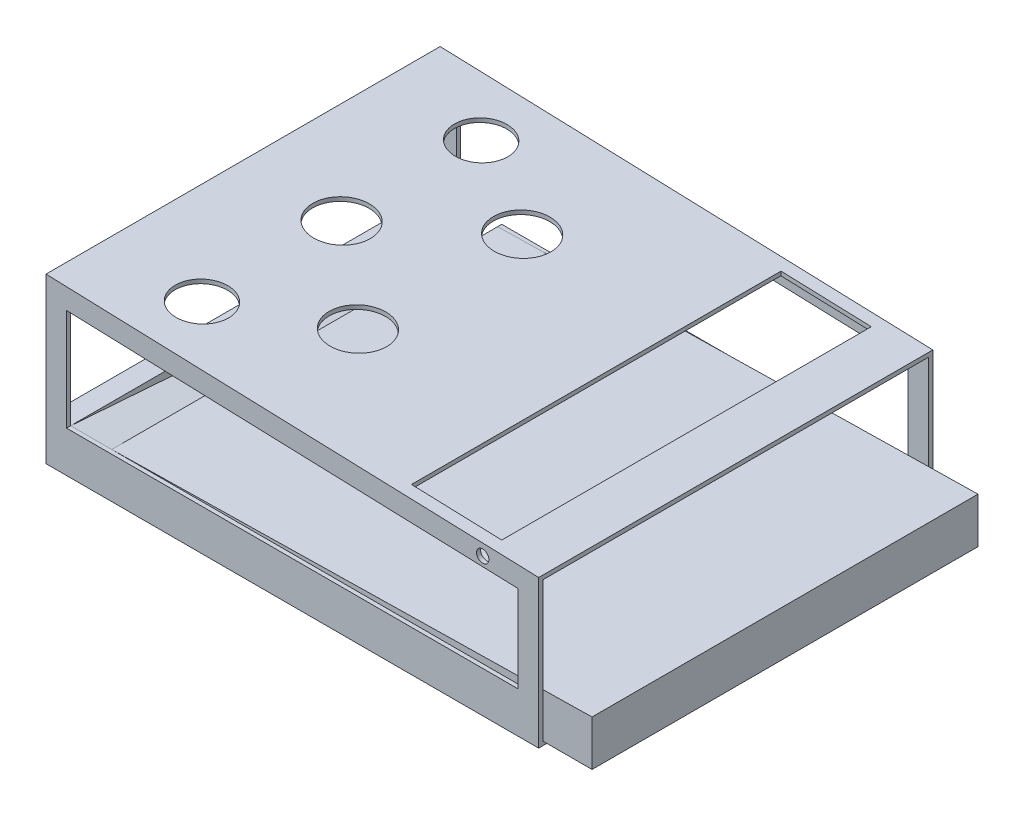
SolidWorks part; units mm, degrees
material "Balsa"
ref_plane "Front Plane" through (0, 0, 0) normal (0, 0, 1) x (1, 0, 0)
ref_plane "Top Plane" through (0, 0, 0) normal (0, 1, 0) x (1, 0, 0)
ref_plane "Right Plane" through (0, 0, 0) normal (1, 0, 0) x (0, 0, -1)
sketch "Sketch1" plane through (0, 0, 0) normal (0, 0, 1) x (1, 0, 0)
  line L0 (-373.9816, 0) -> (388.0184, 0)
  line L1 (-373.9816, 0) -> (-373.9816, 254)
  line L2 (388.0184, 0) -> (388.0184, 228.6)
  line L3 (-373.9816, 254) -> (388.0184, 228.6)
  line L4 (388.0184, 228.6) -> (-373.9816, 228.6) construction
  line L5 (-348.1349, 0) -> (-348.1349, 22.3158) construction
  line L6 (-348.1349, 22.3158) -> (-373.9816, 22.3158) construction
  point P4 (0, 0)
  point P5 (7.0184, 0)
  dimension "D1" = 762
  dimension "D2" = 254
  dimension "D3" = 228.6
extrude "Boss-Extrude1" add sketch "Sketch1" against normal blind 609.6
shell "Shell1" thickness 6.35
sketch "Sketch2" plane through (0, 0, 0) normal (0, 0, 1) x (1, 0, 0)
  line L0 (-342.2316, 221.174) -> (356.2684, 197.8907)
  line L2 (356.2684, 197.8907) -> (356.2684, 63.5)
  line L3 (356.2684, 63.5) -> (-342.2316, 63.5)
  line L4 (-342.2316, 63.5) -> (-342.2316, 221.174)
  line L5 (-373.9816, 0) -> (388.0184, 0) construction
  line L6 (388.0184, 0) -> (388.0184, 228.6) construction
  line L7 (388.0184, 228.6) -> (-373.9816, 254) construction
  line L8 (-373.9816, 254) -> (-373.9816, 0) construction
  point P3 (356.2684, 130.6953)
  dimension "D1" = 63.5
  dimension "D2" = 31.75
  dimension "D3" = 31.75
  dimension "D4" = 31.75
extrude "Cut-Extrude1" cut sketch "Sketch2" against normal up to surface (609.6 mm away) up to face at (7.0184, 120.65, -609.6)
sketch "Sketch5" plane through (0, 0, -603.25) normal (0, 0, 1) x (1, 0, 0)
  line L0 (-373.9816, 132.965) -> (-278.7316, 132.965) construction
  line L1 (-373.9816, 254) -> (-373.9816, 0) construction
  line L2 (-278.7316, 132.965) -> (-278.7316, 63.5) construction
  line L3 (-342.2316, 63.5) -> (356.2684, 63.5) construction
  line L4 (-278.7316, 63.5) -> (464.2184, 76.6965)
  line L5 (388.0184, 63.5) -> (464.2184, 63.5) construction
  line L6 (388.0184, 0) -> (388.0184, 228.6) construction
  line L7 (464.2184, 63.5) -> (464.2184, 76.6965) construction
  line L8 (-278.7316, 63.5) -> (-278.7316, 6.35)
  line L9 (-373.9816, 6.35) -> (388.0184, 6.35) construction
  line L10 (-278.7316, 6.35) -> (464.2184, 6.35)
  line L11 (464.2184, 6.35) -> (464.2184, 76.6965)
  dimension "D1" = 95.25
  dimension "D2" = 76.2
extrude "Boss-Extrude3" add sketch "Sketch5" along normal up to surface (596.9 mm away) up to face at (7.0184, 136.5162, -6.35)
sketch "Sketch6" plane through (-278.7316, 0, 0) normal (-1, 0, 0) x (0, 0, 1)
  line L0 (-6.35, 63.5) -> (-603.25, 19.05)
  line L1 (-603.25, 63.5) -> (-603.25, 6.35) construction
  line L2 (-603.25, 19.05) -> (-603.25, 6.35)
  line L3 (-603.25, 6.35) -> (-6.35, 6.35)
  line L4 (-6.35, 6.35) -> (-6.35, 63.5)
  dimension "D1" = 12.7
extrude "Boss-Extrude4" add sketch "Sketch6" along normal up to surface (95.25 mm away) up to face at (-373.9816, 127, -304.8)
sketch "Sketch8" plane through (0, 0, -609.6) normal (0, 0, -1) x (-1, 0, 0)
  line L1 (342.2316, 63.5) -> (373.9816, 63.5)
  line L2 (342.2316, 63.5) -> (342.2316, 19.05)
  line L3 (342.2316, 19.05) -> (373.9816, 19.05)
  line L4 (373.9816, 63.5) -> (373.9816, 19.05)
extrude "Boss-Extrude5" add sketch "Sketch8" against normal up to surface (603.25 mm away) up to face at (7.0184, 145.76, -6.35)
sketch "Sketch9" plane through (0, 0, -609.6) normal (0, 0, -1) x (-1, 0, 0)
  line L1 (278.7316, 63.5) -> (342.2316, 63.5)
  line L2 (278.7316, 63.5) -> (278.7316, 19.05)
  line L3 (278.7316, 19.05) -> (342.2316, 19.05)
  line L4 (342.2316, 63.5) -> (342.2316, 19.05)
extrude "Cut-Extrude2" cut sketch "Sketch9" against normal up to surface (6.35 mm away) up to face at (-310.4816, 41.275, -603.25)
sketch "Sketch10" plane through (8.0422, 241.2659, 0) normal (0.0333, 0.9994, 0) x (0.9994, -0.0333, 0)
  line L0 (-229.836, 609.6) -> (-229.836, 0) construction
  line L1 (380.1873, 609.6) -> (-382.236, 609.6) construction
  line L2 (380.1873, 0) -> (-382.236, 0) construction
  line L3 (-382.236, 609.6) -> (-382.236, 0) construction
  line L4 (-382.236, 304.8) -> (380.1873, 304.8) construction
  line L5 (380.1873, 609.6) -> (380.1873, 0) construction
  line L6 (-77.436, 609.6) -> (-77.436, 0) construction
  circle A1 centre (-229.836, 88.9) radius 41.275
  circle A2 centre (-229.836, 520.7) radius 41.275
  circle A5 centre (-77.436, 431.8) radius 44.45
  circle A6 centre (-77.436, 177.8) radius 44.45
  circle A7 centre (-229.836, 304.8) radius 44.45
  dimension "D2" = 82.55
  dimension "D7" = 177.8
  dimension "D8" = 88.9
  dimension "D1" = 152.4
  dimension "D4" = 304.8
  dimension "D5" = 88.9
  dimension "D6" = 304.8
extrude "Cut-Extrude3" cut sketch "Sketch10" against normal up to surface (6.35 mm away) up to face at (7.0184, 234.9465, -304.8)
sketch "Sketch12" plane through (8.0422, 241.2659, 0) normal (0.0333, 0.9994, 0) x (0.9994, -0.0333, 0)
  line L0 (303.9873, 0) -> (303.9873, 609.6) construction
  line L1 (380.1873, 0) -> (-382.236, 0) construction
  line L2 (380.1873, 609.6) -> (-382.236, 609.6) construction
  line L3 (380.1873, 609.6) -> (380.1873, 0) construction
  line L4 (303.9873, 19.05) -> (166.1086, 19.05) construction
  line L6 (303.9873, 19.05) -> (164.2873, 19.05)
  line L7 (303.9873, 19.05) -> (303.9873, 590.55)
  line L8 (303.9873, 590.55) -> (164.2873, 590.55)
  line L9 (164.2873, 19.05) -> (164.2873, 590.55)
  dimension "D1" = 76.2
  dimension "D2" = 19.05
  dimension "D3" = 19.05
  dimension "D4" = 571.5
  dimension "D5" = 139.7
extrude "Cut-Extrude4" cut sketch "Sketch12" against normal up to surface (6.35 mm away) up to face at (-113.9876, 238.98, -177.8)
sketch "Sketch13" plane through (0, 0, 0) normal (0, 0, 1) x (1, 0, 0)
  circle A0 centre (301.4678, 213.9904) radius 9.525
  dimension "D1" = 19.05
extrude "Cut-Extrude5" cut sketch "Sketch13" against normal up to surface (609.6 mm away) up to face at (-88.2316, 97.3608, -609.6)
